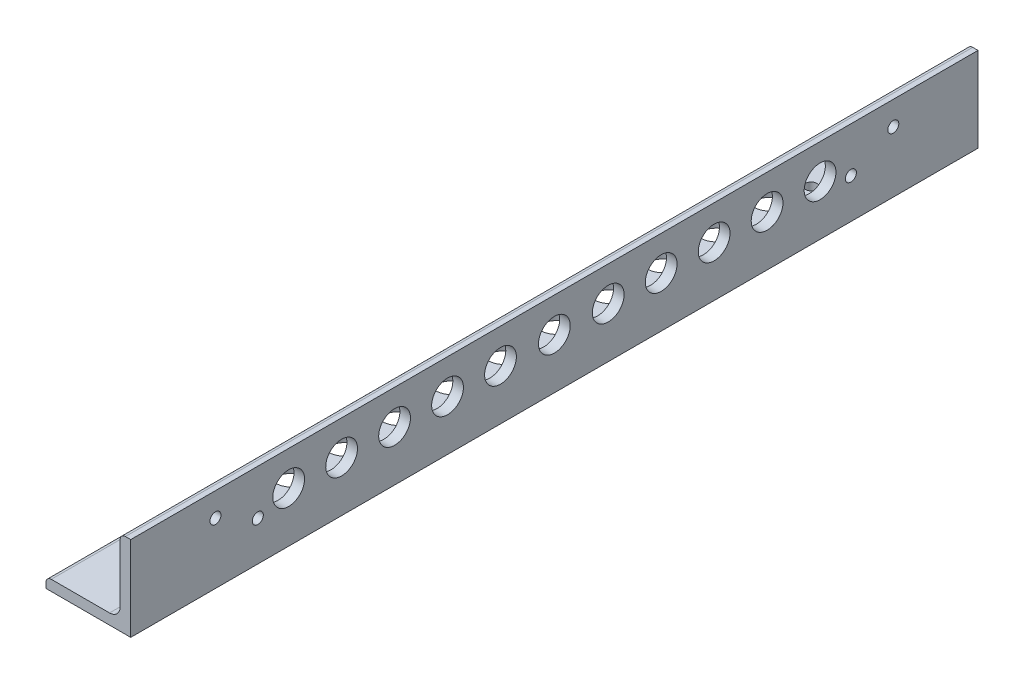
SolidWorks part; units mm, degrees
material "6061-T6 (SS)"
ref_plane "Front Plane" through (0, 0, 0) normal (0, 0, 1) x (1, 0, 0)
ref_plane "Top Plane" through (0, 0, 0) normal (0, 1, 0) x (1, 0, 0)
ref_plane "Right Plane" through (0, 0, 0) normal (1, 0, 0) x (0, 0, -1)
sketch "Sketch0" plane through (0, 0, 0) normal (0, 0, 1) x (1, 0, 0)
  line L0 (-12.7, -12.7) -> (12.7, -12.7)
  line L1 (12.7, -12.7) -> (12.7, 12.7)
  line L2 (12.7, 0) -> (0, 0) construction
  line L3 (0, 0) -> (0, -12.7) construction
  line L4 (9.525, -6.35) -> (9.525, 12.7) construction
  line L5 (6.35, -9.525) -> (-12.7, -9.525) construction
  arc A0 (9.525, -6.35) -> (6.35, -9.525) centre (6.35, -6.35) cw
  point P3 (8.5951, -8.5951)
  dimension "Inside Corner Radius" = 3.175
  dimension "Outside Height" = 25.4
  dimension "Inside Height" = 22.225
  dimension "Inside Width" = 22.225
  dimension "Wall Thickness" = 3.175
  dimension "D1" = 3.175
  dimension "Outside Width" = 25.4
sketch "Sketch1" plane through (0, 0, 0) normal (1, 0, 0) x (0, 0, -1)
  line L0 (127, 0) -> (-127, 0)
  point P4 (0, 0)
  dimension "Length" = 254
sketch "Sketch2" plane through (0, 0, 0) normal (0, 0, 1) x (1, 0, 0)
  line L0 (-12.7, -12.7) -> (12.7, -12.7)
  line L1 (12.7, -12.7) -> (12.7, 12.7)
  line L2 (12.7, 12.7) -> (9.525, 12.7) construction
  line L3 (9.525, 11.1125) -> (9.525, -6.35)
  line L4 (6.35, -9.525) -> (-11.1125, -9.525)
  line L5 (-12.7, -12.7) -> (-12.7, -9.525) construction
  line L6 (11.1125, 12.7) -> (12.7, 12.7)
  line L7 (-12.7, -11.1125) -> (-12.7, -12.7)
  line L8 (12.7, 0) -> (0, 0) construction
  line L9 (0, 0) -> (0, -12.7) construction
  arc A0 (9.525, 11.1125) -> (11.1125, 12.7) centre (11.1125, 11.1125) cw
  arc A1 (-12.7, -11.1125) -> (-11.1125, -9.525) centre (-11.1125, -11.1125) cw
  arc A2 (9.525, -6.35) -> (6.35, -9.525) centre (6.35, -6.35) cw
  dimension "Inside Radius" = 3.175
  dimension "Height" = 25.4
  dimension "Width" = 25.4
  dimension "Thickness" = 3.175
extrude "Boss-Extrude1" add sketch "Sketch2" along normal mid plane 254
sketch "Break Locations" plane through (0, 0, 0) normal (1, 0, 0) x (0, 0, -1)
  line L0 (-101.092, 0) -> (101.092, 0)
  line L1 (-127, -12.7) -> (-127, 12.7) construction
  line L2 (127, -12.7) -> (127, 12.7) construction
  point P0 (-105.41, 0)
  point P1 (105.41, 0)
  point P10 (0, 0)
  point P11 (101.092, 0)
  point P13 (-101.092, 0)
  dimension "D1" = 21.59
  dimension "D2" = 21.59
  dimension "D3" = 25.908
sketch "Sketch4" plane through (0, -9.525, 0) normal (0, 1, 0) x (1, 0, 0)
  line L0 (6.35, 0) -> (-11.1125, 0) construction
  line L1 (6.35, -127) -> (6.35, 127) construction
  line L2 (-11.1125, -127) -> (-11.1125, 127) construction
  line L3 (-2.3812, 127) -> (-2.3812, 101.6) construction
  line L4 (6.35, 127) -> (-11.1125, 127) construction
  line L5 (-2.3812, 101.6) -> (-5.5562, 101.6) construction
  line L6 (0.7938, 88.9079) -> (0.7938, 76.2079) construction
  line L7 (-2.3812, 101.6) -> (0.7938, 101.6) construction
  line L8 (0.7938, 101.6) -> (0.7938, 88.9079) construction
  line L9 (0.7938, 88.9079) -> (-2.3812, 88.9079) construction
  line L10 (-2.3812, 88.9079) -> (-2.3812, 79.6623) construction
  line L11 (-2.3812, 79.6623) -> (-2.3812, 63.7873) construction
  circle A0 centre (-5.5562, 101.6) radius 1.651
  circle A1 centre (0.7938, 88.9079) radius 1.651
  circle A2 centre (0.7938, -88.9079) radius 1.651
  circle A3 centre (-5.5562, -101.6) radius 1.651
  circle A4 centre (-2.3812, 79.6623) radius 4.7625
  circle A5 centre (-2.3812, 63.6603) radius 4.7625
  circle A6 centre (-2.3812, 47.6583) radius 4.7625
  circle A7 centre (-2.3812, 31.6563) radius 4.7625
  circle A8 centre (-2.3812, 15.6543) radius 4.7625
  circle A9 centre (-2.3812, 0) radius 4.7625
  circle A10 centre (-2.3812, -15.6543) radius 4.7625
  circle A11 centre (-2.3812, -31.6563) radius 4.7625
  circle A12 centre (-2.3812, -47.6583) radius 4.7625
  circle A13 centre (-2.3812, -63.6603) radius 4.7625
  circle A14 centre (-2.3812, -79.6623) radius 4.7625
  point P13 (-2.3812, 101.6)
  dimension "D3" = 3.302
  dimension "D4" = 3.302
  dimension "D9" = 9.525
  dimension "D11" = 9.525
  dimension "D1" = 25.4
  dimension "D2" = 12.7
  dimension "D5" = 3.175
  dimension "D6" = 12.6921
  dimension "D7" = 3.175
  dimension "D8" = 9.2456
  dimension "D10" = 15.875
  dimension "D12" = 5
extrude "Cut-Extrude1" cut sketch "Sketch4" against normal through all
sketch "Sketch5" plane through (9.525, 0, 0) normal (-1, 0, 0) x (0, 0, 1)
  line L0 (-127, 2.3812) -> (-101.6, 2.3812) construction
  line L1 (-127, 11.1125) -> (-127, -6.35) construction
  line L2 (-101.6, -0.7938) -> (-101.6, 2.3812) construction
  line L3 (0, 11.1125) -> (0, -6.35) construction
  line L4 (127, 11.1125) -> (-127, 11.1125) construction
  line L5 (127, -6.35) -> (-127, -6.35) construction
  line L6 (101.6, 2.3812) -> (101.6, 5.5562) construction
  line L7 (-101.6, -0.7938) -> (-88.9, -0.7938) construction
  line L8 (-101.6, 2.3812) -> (-101.6, 5.5562) construction
  line L9 (101.6, -0.7938) -> (88.9, -0.7938) construction
  line L10 (101.6, -0.7938) -> (101.6, 2.3812) construction
  line L11 (127, 2.3812) -> (101.6, 2.3812) construction
  line L12 (-85.9018, 2.3812) -> (-79.6504, 2.3812) construction
  line L13 (-79.6504, 2.3812) -> (-63.7754, 2.3812) construction
  line L14 (-63.7754, 2.3812) -> (-47.9004, 2.3812) construction
  line L15 (-47.9004, 2.3812) -> (-32.0254, 2.3812) construction
  line L16 (-32.0254, 2.3812) -> (-16.1504, 2.3812) construction
  circle A0 centre (-88.9, -0.7938) radius 1.651
  circle A5 centre (-101.6, 5.5562) radius 1.651
  circle A6 centre (88.9, -0.7938) radius 1.651
  circle A7 centre (101.6, 5.5562) radius 1.651
  circle A8 centre (-79.6504, 2.3812) radius 4.7625
  circle A9 centre (-63.7754, 2.3812) radius 4.7625
  circle A10 centre (-47.9004, 2.3812) radius 4.7625
  circle A11 centre (-32.0254, 2.3812) radius 4.7625
  circle A12 centre (-16.1504, 2.3812) radius 4.7625
  circle A13 centre (0, 2.3812) radius 4.7625
  circle A14 centre (16.1504, 2.3812) radius 4.7625
  circle A15 centre (32.0254, 2.3812) radius 4.7625
  circle A16 centre (47.9004, 2.3812) radius 4.7625
  circle A17 centre (63.7754, 2.3812) radius 4.7625
  circle A18 centre (79.6504, 2.3812) radius 4.7625
  point P7 (-101.6, 2.3812)
  point P25 (101.6, 2.3812)
  dimension "D3" = 3.302
  dimension "D4" = 3.302
  dimension "D7" = 9.525
  dimension "D9" = 9.525
  dimension "D13" = 9.525
  dimension "D14" = 9.525
  dimension "D15" = 9.525
  dimension "D1" = 25.4
  dimension "D2" = 3.175
  dimension "D5" = 3.175
  dimension "D6" = 12.7
  dimension "D8" = 15.875
  dimension "D10" = 15.875
  dimension "D11" = 15.875
  dimension "D12" = 15.875
extrude "Cut-Extrude2" cut sketch "Sketch5" against normal through all
equation "\"D1@Break Locations\" = .85 * \"Height@Sketch2\""
equation "\"D2@Break Locations\"=\"D1@Break Locations\""
equation "\"Thickness@Sketch2\"=\"wall thickness@sketch0\""
equation "\"Height@Sketch2\"=\"outside height@sketch0\""
equation "\"Width@Sketch2\"=\"outside width@sketch0\""
equation "\"Inside Radius@Sketch2\"=\"inside corner radius@sketch0\""
equation "\"Length@Boss-Extrude1\"=\"length@sketch1\""
equation "\"D3@Break Locations\"=\"D2@Break Locations\"*1.2"
equation "\"D1@Sketch0\"=\"Wall Thickness@Sketch0\""
